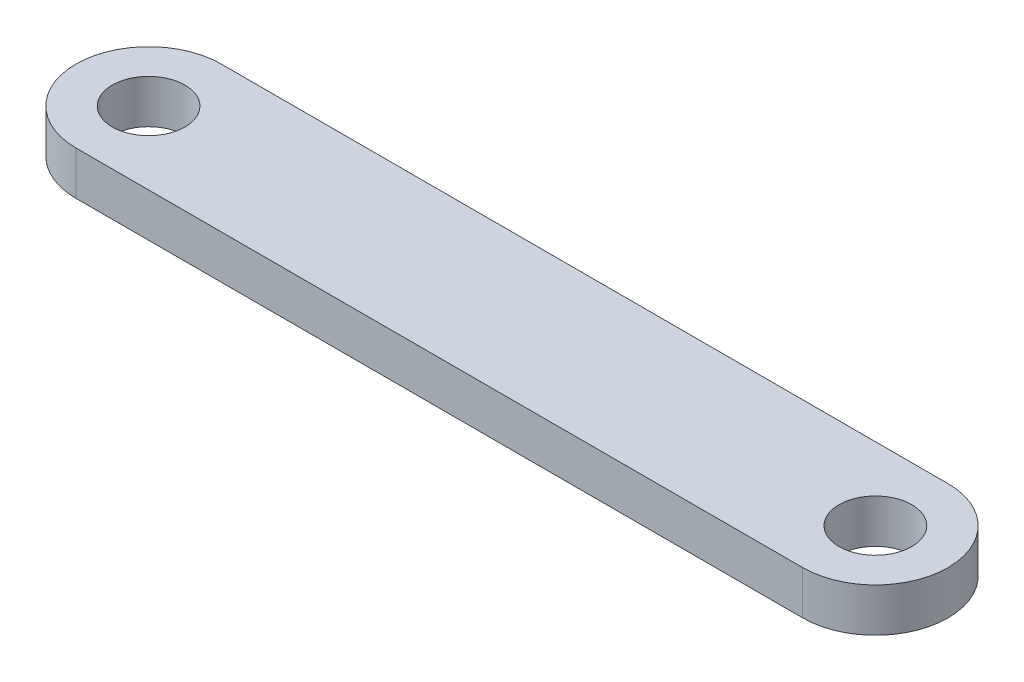
SolidWorks part; units mm, degrees
ref_plane "Alzado" through (0, 0, 0) normal (0, 0, 1) x (1, 0, 0)
ref_plane "Planta" through (0, 0, 0) normal (0, 1, 0) x (1, 0, 0)
ref_plane "Vista lateral" through (0, 0, 0) normal (1, 0, 0) x (0, 0, -1)
sketch "Croquis1" plane through (0, 0, 0) normal (0, 1, 0) x (1, 0, 0)
  line L0 (-25, 0) -> (25, 0) construction
  line L1 (-25, 5) -> (25, 5)
  line L2 (-25, -5) -> (25, -5)
  arc A0 (-25, 5) -> (-25, -5) centre (-25, 0) ccw
  arc A1 (25, -5) -> (25, 5) centre (25, 0) ccw
  circle A2 centre (-25, 0) radius 2.5
  circle A3 centre (25, 0) radius 2.5
  point P3 (0, 0)
  dimension "D2" = 5
  dimension "D3" = 5
  dimension "D1" = 50
extrude "Saliente-Extruir1" add sketch "Croquis1" along normal blind 3
